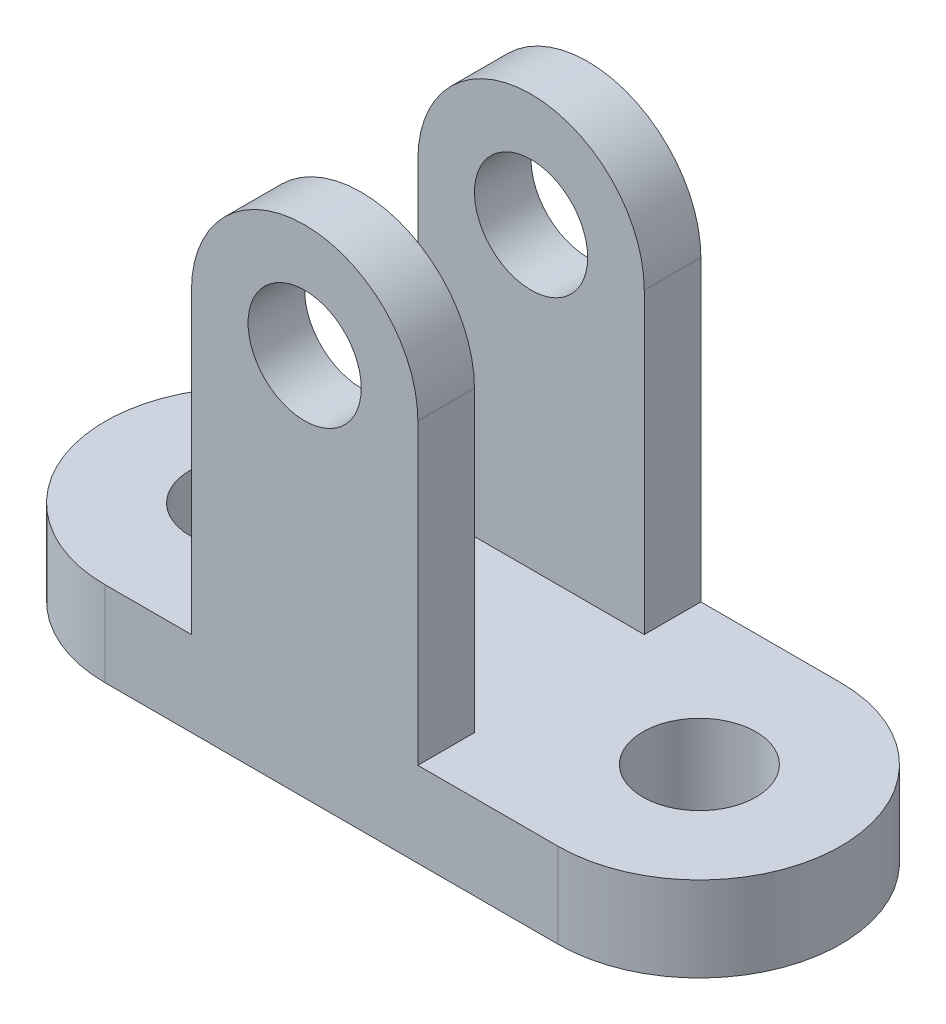
SolidWorks part; units mm, degrees
ref_plane "Front Plane" through (0, 0, 0) normal (0, 0, 1) x (1, 0, 0)
ref_plane "Top Plane" through (0, 0, 0) normal (0, 1, 0) x (1, 0, 0)
ref_plane "Right Plane" through (0, 0, 0) normal (1, 0, 0) x (0, 0, -1)
sketch "Sketch2" plane through (0, 0, 0) normal (0, 1, 0) x (1, 0, 0)
  line L0 (-35.2584, 0) -> (44.7416, 0) construction
  line L1 (-35.2584, 25) -> (44.7416, 25)
  line L2 (-35.2584, -25) -> (44.7416, -25)
  arc A0 (-35.2584, 25) -> (-35.2584, -25) centre (-35.2584, 0) ccw
  arc A1 (44.7416, -25) -> (44.7416, 25) centre (44.7416, 0) ccw
  circle A2 centre (-35.2584, 0) radius 10
  circle A3 centre (44.7416, 0) radius 10
  point P3 (4.7416, 0)
  dimension "D2" = 25
  dimension "D3" = 20
  dimension "D1" = 80
extrude "Boss-Extrude1" add sketch "Sketch2" along normal blind 15
sketch "Sketch4" plane through (0, 0, 25) normal (0, 0, 1) x (1, 0, 0)
  line L0 (-35.2584, 15) -> (44.7416, 15) construction
  line L2 (-20, 67.6995) -> (-20, 15)
  line L3 (-20, 15) -> (20, 15)
  line L4 (20, 67.6995) -> (20, 15)
  arc A0 (20, 67.6995) -> (-20, 67.6995) centre (0, 67.6995) ccw
  circle A1 centre (0, 67.6995) radius 10
  dimension "D1" = 40
  dimension "D2" = 20
extrude "Boss-Extrude2" add sketch "Sketch4" against normal blind 50
sketch "Sketch5" plane through (0, 0, 0) normal (1, 0, 0) x (0, 0, -1)
  line L0 (25, 87.6995) -> (-25, 87.6995) construction
  line L1 (-15, 87.6995) -> (15, 87.6995)
  line L2 (-15, 87.6995) -> (-15, 15)
  line L3 (-15, 15) -> (15, 15)
  line L4 (15, 87.6995) -> (15, 15)
  line L5 (25, 15) -> (-25, 15) construction
  line L6 (-25, 15) -> (-25, 67.6995) construction
  line L7 (25, 15) -> (25, 67.6995) construction
  dimension "D1" = 10
  dimension "D2" = 10
extrude "Cut-Extrude1" cut sketch "Sketch5" against normal mid plane 50
